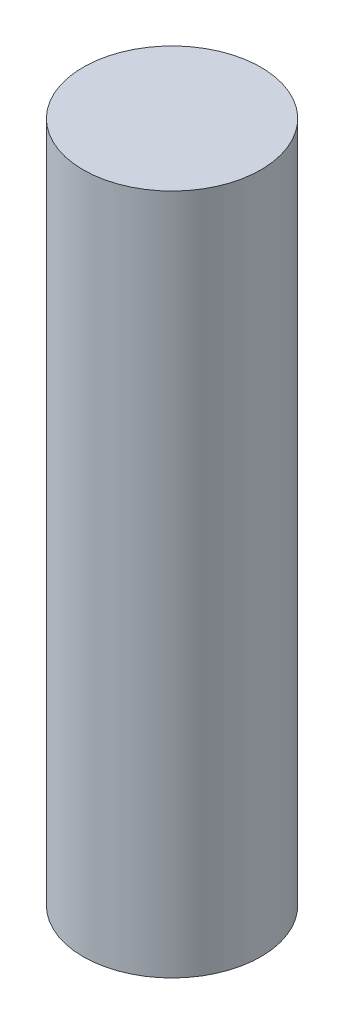
SolidWorks part; units mm, degrees
ref_plane "Front Plane" through (0, 0, 0) normal (0, 0, 1) x (1, 0, 0)
ref_plane "Top Plane" through (0, 0, 0) normal (0, 1, 0) x (1, 0, 0)
ref_plane "Right Plane" through (0, 0, 0) normal (1, 0, 0) x (0, 0, -1)
sketch "Sketch1" plane through (0, 0, 0) normal (0, 1, 0) x (1, 0, 0)
  circle A0 centre (0, 0) radius 9
  dimension "D1" = 18
extrude "Boss-Extrude1" add sketch "Sketch1" along normal blind 69
